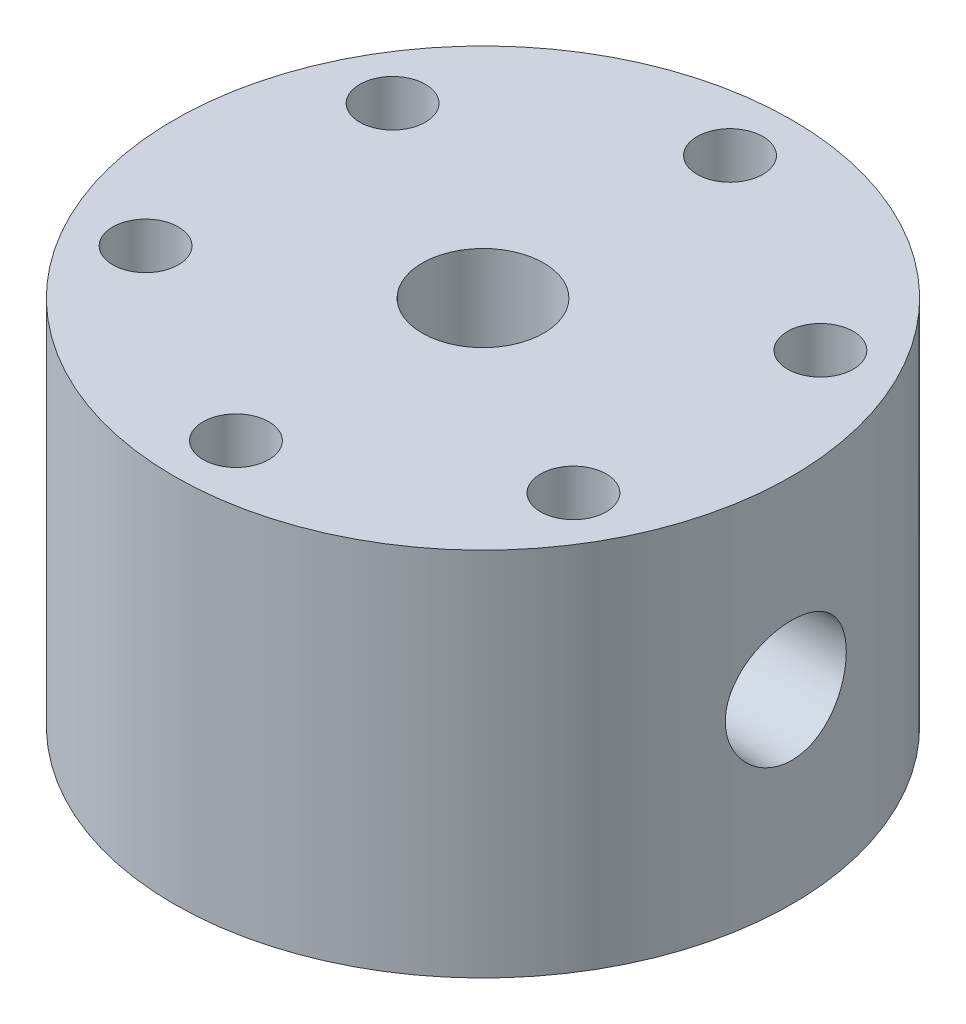
SolidWorks part; units mm, degrees
ref_plane "Front Plane" through (0, 0, 0) normal (0, 0, 1) x (1, 0, 0)
ref_plane "Top Plane" through (0, 0, 0) normal (0, 1, 0) x (1, 0, 0)
ref_plane "Right Plane" through (0, 0, 0) normal (1, 0, 0) x (0, 0, -1)
sketch "Sketch1" plane through (0, 0, 0) normal (0, 0, 1) x (1, 0, 0)
  line L2 (-3.81, 0) -> (-8.0645, 0)
  line L3 (-31.75, -6.35) -> (-31.75, 31.75)
  line L4 (-31.75, 31.75) -> (-3.81, 31.75)
  line L6 (-3.81, 31.75) -> (-3.81, 0)
  line L10 (0, 0) -> (0, 15.7692) construction
  line L11 (-31.75, -6.35) -> (-12.7, -6.35)
  line L12 (-11.1125, 0) -> (-11.1125, 2.032)
  line L13 (-11.1125, 2.032) -> (-8.0645, 2.032)
  line L14 (-8.0645, 2.032) -> (-8.0645, 0)
  line L15 (-11.1125, 0) -> (-12.7, 0)
  line L16 (-12.7, 0) -> (-12.7, -6.35)
  dimension "D1" = 3.81
  dimension "D2" = 1.5875
  dimension "D3" = 12.7
  dimension "D4" = 38.1
  dimension "D5" = 31.75
  dimension "D6" = 6.35
  dimension "D8" = 3.048
  dimension "D9" = 2.032
revolve "Revolve1" add sketch "Sketch1" angle 360 about L10
hole_wizard "M14x1.5 Tapped Hole1" positions "Sketch2" profile "Sketch4" tap size "M14x1.5" standard "ANSI Metric"
sketch "Sketch2" plane through (0, 31.75, 0) normal (0, 1, 0) x (1, 0, 0)
  point P0 (0, 0)
sketch "Sketch4" plane through (0, 31.75, 0) normal (1, 0, 0) x (0, 0, 1)
  line L0 (0, 0) -> (0, 29.1554)
  line L1 (0, 29.1554) -> (6.25, 25.4)
  line L2 (6.25, 25.4) -> (6.25, 0)
  line L5 (6.25, 0) -> (0, 0)
  line L10 (0, 29.1554) -> (-6.25, 25.4) construction
  line L11 (0, -6.35) -> (0, 107.95) construction
  dimension "Tap Drill Dia." = 12.5
  dimension "Tap Drill Depth" = 25.4
  dimension "Drill Angle" = 118
cosmetic thread "Hole Thread3" parameters "D1"=27.94, "D2"=14
ref_plane "Plane1" through (31.75, 0, 0) normal (1, 0, 0) x (0, 0, -1)
ref_plane "Plane2" through (-31.75, 0, 0) normal (-1, 0, 0) x (0, 0, 1)
hole_wizard "1/4 NPT Tapped Hole1" positions "Sketch5" profile "Sketch6" size "1/4" standard "ANSI Inch"
sketch "Sketch5" plane through (31.75, 0, 0) normal (1, 0, 0) x (0, 0, -1)
  line L0 (31.75, 31.75) -> (-31.75, 31.75) construction
  point P0 (0, 12.7)
  dimension "D1" = 19.05
sketch "Sketch6" plane through (31.75, 12.7, 0) normal (0, 1, 0) x (0, 0, -1)
  line L0 (0, 0) -> (0, 20.3603)
  line L1 (5.5626, 17.018) -> (0, 20.3603)
  line L2 (-5.5626, 17.018) -> (0, 20.3603) construction
  line L3 (5.5626, 17.018) -> (5.5626, 9.906)
  line L4 (5.5626, 9.906) -> (5.9437, 9.906)
  line L5 (5.9437, 9.906) -> (6.2403, 0)
  line L6 (-5.9437, 9.906) -> (-6.2403, 0) construction
  line L7 (6.2403, 0) -> (0, 0)
  line L8 (0, -6.35) -> (0, 107.95) construction
  line L11 (-5.5626, 9.906) -> (-5.9437, 9.906) construction
  dimension "Tap Drill Dia." = 11.1252
  dimension "Tap Drill Depth" = 17.018
  dimension "Thread Dia." = 12.4806
  dimension "Thread Angle" = 3.43
  dimension "Thread Depth" = 9.906
  dimension "Drill Angle" = 118
cosmetic thread "Hole Thread1" parameters "D1"=9.906, "D2"=13.7086
hole_wizard "1/4 NPT Tapped Hole2" positions "Sketch7" profile "Sketch8" size "1/4" standard "ANSI Inch"
sketch "Sketch7" plane through (-31.75, 0, 0) normal (-1, 0, 0) x (0, 0, 1)
  line L0 (31.75, 31.75) -> (-31.75, 31.75) construction
  point P0 (0, 12.7)
  dimension "D1" = 19.05
sketch "Sketch8" plane through (-31.75, 12.7, 0) normal (0, 1, 0) x (0, 0, 1)
  line L0 (0, 0) -> (0, 20.3603)
  line L1 (5.5626, 17.018) -> (0, 20.3603)
  line L2 (-5.5626, 17.018) -> (0, 20.3603) construction
  line L3 (5.5626, 17.018) -> (5.5626, 9.906)
  line L4 (5.5626, 9.906) -> (5.9437, 9.906)
  line L5 (5.9437, 9.906) -> (6.2403, 0)
  line L6 (-5.9437, 9.906) -> (-6.2403, 0) construction
  line L7 (6.2403, 0) -> (0, 0)
  line L8 (0, -6.35) -> (0, 107.95) construction
  line L11 (-5.5626, 9.906) -> (-5.9437, 9.906) construction
  dimension "Tap Drill Dia." = 11.1252
  dimension "Tap Drill Depth" = 17.018
  dimension "Thread Dia." = 12.4806
  dimension "Thread Angle" = 3.43
  dimension "Thread Depth" = 9.906
  dimension "Drill Angle" = 118
cosmetic thread "Hole Thread2" parameters "D1"=9.906, "D2"=13.7086
hole_wizard "1/16 (0.0625) Diameter Hole1" positions "Sketch9" profile "Sketch10" hole size "1/16" standard "ANSI Inch"
sketch "Sketch9" plane through (31.75, 0, 0) normal (1, 0, 0) x (0, 0, -1)
  point P0 (0, 12.7)
sketch "Sketch10" plane through (31.75, 12.7, 0) normal (0, 1, 0) x (0, 0, -1)
  line L0 (0, 0) -> (0, 29.0519)
  line L1 (0, 29.0519) -> (0.7937, 28.575)
  line L2 (0.7937, 28.575) -> (0.7937, 0)
  line L5 (0.7937, 0) -> (0, 0)
  line L10 (0, 29.0519) -> (-0.7938, 28.575) construction
  line L11 (0, -6.35) -> (0, 107.95) construction
  dimension "Hole Dia." = 1.5875
  dimension "Hole Depth" = 28.575
  dimension "Drill Angle" = 118
hole_wizard "3/32 (0.09375) Diameter Hole1" positions "Sketch11" profile "Sketch12" hole size "3/32" standard "ANSI Inch"
sketch "Sketch11" plane through (-31.75, 0, 0) normal (-1, 0, 0) x (0, 0, 1)
  point P0 (0, 12.7)
sketch "Sketch12" plane through (-31.75, 12.7, 0) normal (0, 1, 0) x (0, 0, 1)
  line L0 (0, 0) -> (0, 29.4174)
  line L1 (0, 29.4174) -> (1.1906, 28.702)
  line L2 (1.1906, 28.702) -> (1.1906, 0)
  line L5 (1.1906, 0) -> (0, 0)
  line L10 (0, 29.4174) -> (-1.1906, 28.702) construction
  line L11 (0, -6.35) -> (0, 107.95) construction
  dimension "Hole Dia." = 2.3812
  dimension "Hole Depth" = 28.702
  dimension "Drill Angle" = 118
hole_wizard "1/4 Clearance Hole1" positions "Sketch15" profile "Sketch16" hole size "1/4" standard "ANSI Inch" end condition through all
sketch "Sketch15" plane through (0, 31.75, 0) normal (0, 1, 0) x (1, 0, 0)
  line L0 (0, 0) -> (16.0984, 0) construction
  line L2 (0, 0) -> (21.997, 12.7) construction
  point P0 (21.997, 12.7)
  dimension "D1" = 25.4
  dimension "D2" = 30
sketch "Sketch16" plane through (21.997, 31.75, -12.7) normal (1, 0, 0) x (0, 0, 1)
  line L0 (0, 0) -> (0, 38.1)
  line L1 (0, 38.1) -> (3.3782, 38.1)
  line L2 (3.3782, 38.1) -> (3.3782, 0)
  line L5 (3.3782, 0) -> (0, 0)
  line L11 (0, -6.35) -> (0, 107.95) construction
  dimension "Thru Hole Dia." = 6.7564
  dimension "Thru Hole Depth" = 38.1
pattern_circular "CirPattern1" count 6 over 360 about axis through (0, 0, 0) along (0, 1, 0) of "1/4 Clearance Hole1"
ref_plane "Plane3" through (15.875, 0, -27.4963) normal (0.5, 0, -0.866) x (0, -1, 0)
hole_wizard "1/4 NPT Tapped Hole3" positions "Sketch17" profile "Sketch18" size "1/4" standard "ANSI Inch"
sketch "Sketch17" plane through (15.875, 0, -27.4963) normal (0.5, 0, -0.866) x (0, -1, 0)
  point P0 (-12.7, 0)
  dimension "D1" = 12.7
sketch "Sketch18" plane through (15.875, 12.7, -27.4963) normal (0, 1, 0) x (-0.866, 0, -0.5)
  line L0 (0, 0) -> (0, 19.8523)
  line L1 (5.5626, 16.51) -> (0, 19.8523)
  line L2 (-5.5626, 16.51) -> (0, 19.8523) construction
  line L3 (5.5626, 16.51) -> (5.5626, 12.7)
  line L4 (5.5626, 12.7) -> (6.558, 12.7)
  line L5 (6.558, 12.7) -> (6.9382, 0)
  line L6 (-6.558, 12.7) -> (-6.9382, 0) construction
  line L7 (6.9382, 0) -> (0, 0)
  line L8 (0, -6.35) -> (0, 107.95) construction
  line L11 (-5.5626, 12.7) -> (-6.558, 12.7) construction
  dimension "Tap Drill Dia." = 11.1252
  dimension "Tap Drill Depth" = 16.51
  dimension "Thread Dia." = 13.8765
  dimension "Thread Angle" = 3.43
  dimension "Thread Depth" = 12.7
  dimension "Drill Angle" = 118
hole_wizard "1/32 (0.03125) Diameter Hole1" positions "Sketch19" profile "Sketch20" hole size "1/32" standard "ANSI Inch"
sketch "Sketch19" plane through (15.875, 0, -27.4963) normal (0.5, 0, -0.866) x (0, -1, 0)
  point P0 (-12.7, 0)
sketch "Sketch20" plane through (15.875, 12.7, -27.4963) normal (0, 1, 0) x (-0.866, 0, -0.5)
  line L0 (0, 0) -> (0, 28.8135)
  line L1 (0, 28.8135) -> (0.3969, 28.575)
  line L2 (0.3969, 28.575) -> (0.3969, 0)
  line L5 (0.3969, 0) -> (0, 0)
  line L10 (0, 28.8135) -> (-0.3969, 28.575) construction
  line L11 (0, -6.35) -> (0, 107.95) construction
  dimension "Hole Dia." = 0.7937
  dimension "Hole Depth" = 28.575
  dimension "Drill Angle" = 118
